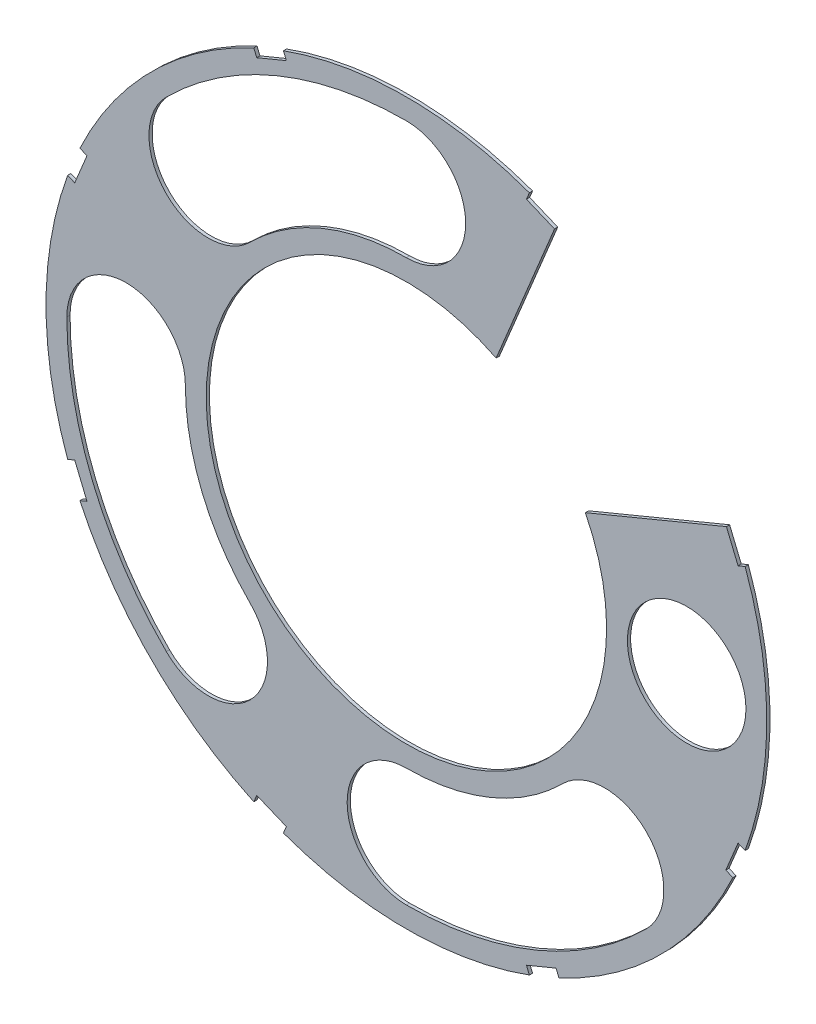
SolidWorks part; units mm, degrees
material "PTFE (general)"
ref_plane "Front Plane" through (0, 0, 0) normal (0, 0, 1) x (1, 0, 0)
ref_plane "Top Plane" through (0, 0, 0) normal (0, 1, 0) x (1, 0, 0)
ref_plane "Right Plane" through (0, 0, 0) normal (1, 0, 0) x (0, 0, -1)
sketch "Sketch4" plane through (0, 0, 0) normal (0, 0, 1) x (1, 0, 0)
  circle A0 centre (0, 0) radius 28.575
  dimension "D1" = 57.15
extrude "Boss-Extrude2" add sketch "Sketch4" along normal blind 0.254
sketch "Sketch5" plane through (0, 0, 0.254) normal (0, 0, 1) x (1, 0, 0)
  circle A0 centre (0, 0) radius 15.875
  circle A1 centre (0, 0) radius 28.575 construction
  dimension "D1" = 12.7
extrude "Cut-Extrude5" cut sketch "Sketch5" against normal through all
sketch "Sketch6" plane through (0, 0, 0.254) normal (0, 0, 1) x (1, 0, 0)
  line L0 (0, 0) -> (22.225, 0) construction
  line L1 (0, 0) -> (20.2056, -20.2056) construction
  line L2 (0, 0) -> (0, -28.575) construction
  line L3 (0, 0) -> (0, -28.575) construction
  line L4 (0, 0) -> (20.2056, -20.2056) construction
  line L5 (0, 0) -> (-20.2056, -20.2056) construction
  line L6 (0, 0) -> (-20.2056, -20.2056) construction
  line L7 (0, 0) -> (-28.575, 0) construction
  line L8 (0, 0) -> (-28.575, 0) construction
  line L9 (0, 0) -> (-20.2056, 20.2056) construction
  line L10 (0, 0) -> (-20.2056, 20.2056) construction
  line L11 (0, 0) -> (0, 28.575) construction
  line L12 (0, 0) -> (0, 28.575) construction
  line L13 (0, 0) -> (12.3928, -12.3928) construction
  line L14 (0, 0) -> (-12.3928, -12.3928) construction
  circle A0 centre (22.225, 0) radius 4.699
  circle A1 centre (0, 0) radius 28.575 construction
  arc A2 (19.0381, -19.0381) -> (12.3928, -12.3928) centre (15.7154, -15.7154) ccw
  arc A3 (12.3928, -12.3928) -> (0, -17.526) centre (0, 0) cw
  arc A4 (0, -17.526) -> (0, -26.924) centre (0, -22.225) ccw
  arc A5 (0, -26.924) -> (19.0381, -19.0381) centre (0, 0) ccw
  arc A6 (-19.0381, -19.0381) -> (-12.3928, -12.3928) centre (-15.7154, -15.7154) ccw
  arc A7 (-12.3928, -12.3928) -> (-17.526, 0) centre (0, 0) cw
  arc A8 (-26.924, 0) -> (-19.0381, -19.0381) centre (0, 0) ccw
  arc A9 (-17.526, 0) -> (-26.924, 0) centre (-22.225, 0) ccw
  arc A10 (-19.0381, 19.0381) -> (-12.3928, 12.3928) centre (-15.7154, 15.7154) ccw
  arc A11 (-12.3928, 12.3928) -> (0, 17.526) centre (0, 0) cw
  arc A12 (0, 26.924) -> (-19.0381, 19.0381) centre (0, 0) ccw
  arc A13 (0, 17.526) -> (0, 26.924) centre (0, 22.225) ccw
  circle A16 centre (0, 0) radius 15.875 construction
  point P4 (15.7154, -15.7154)
  point P11 (0, -22.225)
  point P13 (-15.7154, -15.7154)
  point P27 (-22.225, 0)
  point P30 (0, 0)
  point P36 (-15.7154, 15.7154)
  point P41 (0, 22.225)
  dimension "D2" = 9.398
  dimension "D3" = 45
  dimension "D4" = 90
  dimension "D1" = 6.35
  dimension "D6" = 6.35
  dimension "D7" = 9.398
  dimension "D8" = 4.699
  dimension "D9" = 4.699
  dimension "D5" = 6.35
  dimension "D10" = 90
extrude "Cut-Extrude6" cut sketch "Sketch6" against normal through all
sketch "Sketch8" plane through (0, 0, 0.254) normal (0, 0, 1) x (1, 0, 0)
  line L0 (0, 0) -> (26.3999, 10.9352) construction
  line L1 (0, 0) -> (10.9352, 26.3999) construction
  line L2 (11.7482, 25.3758) -> (9.5188, 26.2992)
  line L3 (25.3758, 11.7482) -> (26.2992, 9.5188)
  line L4 (26.8598, 9.751) -> (26.2992, 9.5188)
  line L5 (9.751, 26.8598) -> (9.5188, 26.2992)
  line L6 (0, 0) -> (28.575, 0) construction
  line L7 (-10.0049, 27.4725) -> (-12.3515, 26.5005)
  line L8 (-10.0049, 27.4725) -> (-9.5188, 26.2992)
  line L9 (-12.3515, 26.5005) -> (-11.8655, 25.3272)
  line L10 (-9.5188, 26.2992) -> (-11.8655, 25.3272)
  line L11 (-12.3515, 26.5005) -> (-9.5188, 26.2992) construction
  line L12 (-10.0049, 27.4725) -> (-11.8655, 25.3272) construction
  line L13 (-26.5005, 12.3515) -> (-27.4725, 10.0049)
  line L14 (-26.5005, 12.3515) -> (-25.3272, 11.8655)
  line L15 (-25.3272, 11.8655) -> (-26.2992, 9.5188)
  line L16 (-27.4725, 10.0049) -> (-26.2992, 9.5188)
  line L17 (-26.5005, 12.3515) -> (-26.2992, 9.5188) construction
  line L18 (-27.4725, 10.0049) -> (-25.3272, 11.8655) construction
  line L19 (-27.4725, -10.0049) -> (-26.5005, -12.3515)
  line L20 (-27.4725, -10.0049) -> (-26.2992, -9.5188)
  line L21 (-26.2992, -9.5188) -> (-25.3272, -11.8655)
  line L22 (-26.5005, -12.3515) -> (-25.3272, -11.8655)
  line L23 (-27.4725, -10.0049) -> (-25.3272, -11.8655) construction
  line L24 (-26.5005, -12.3515) -> (-26.2992, -9.5188) construction
  line L25 (-12.3515, -26.5005) -> (-10.0049, -27.4725)
  line L26 (-12.3515, -26.5005) -> (-11.8655, -25.3272)
  line L27 (-11.8655, -25.3272) -> (-9.5188, -26.2992)
  line L28 (-10.0049, -27.4725) -> (-9.5188, -26.2992)
  line L29 (-12.3515, -26.5005) -> (-9.5188, -26.2992) construction
  line L30 (-10.0049, -27.4725) -> (-11.8655, -25.3272) construction
  line L31 (10.0049, -27.4725) -> (12.3515, -26.5005)
  line L32 (10.0049, -27.4725) -> (9.5188, -26.2992)
  line L33 (9.5188, -26.2992) -> (11.8655, -25.3272)
  line L34 (12.3515, -26.5005) -> (11.8655, -25.3272)
  line L35 (10.0049, -27.4725) -> (11.8655, -25.3272) construction
  line L36 (12.3515, -26.5005) -> (9.5188, -26.2992) construction
  line L37 (26.5005, -12.3515) -> (27.4725, -10.0049)
  line L38 (26.5005, -12.3515) -> (25.3272, -11.8655)
  line L39 (25.3272, -11.8655) -> (26.2992, -9.5188)
  line L40 (27.4725, -10.0049) -> (26.2992, -9.5188)
  line L41 (26.5005, -12.3515) -> (26.2992, -9.5188) construction
  line L42 (27.4725, -10.0049) -> (25.3272, -11.8655) construction
  line L43 (14.1911, 7.1153) -> (25.3758, 11.7482)
  line L44 (7.1153, 14.1911) -> (11.7482, 25.3758)
  circle A0 centre (0, 0) radius 28.575 construction
  arc A1 (14.1911, 7.1153) -> (7.1153, 14.1911) centre (0, 0) ccw
  circle A2 centre (0, 0) radius 15.875 construction
  arc A3 (26.8598, 9.751) -> (9.751, 26.8598) centre (0, 0) ccw
  point P3 (-10.9352, 26.3999)
  point P11 (-26.3999, 10.9352)
  point P20 (-26.3999, -10.9352)
  point P25 (-10.9352, -26.3999)
  point P26 (0, 0)
  point P31 (10.9352, -26.3999)
  point P36 (26.3999, -10.9352)
  point P46 (0, 0)
  dimension "D4" = 90
  dimension "D19" = 28.575
  dimension "D2" = 67.5
  dimension "D3" = 22.5
  dimension "D5" = 1.27
  dimension "D6" = 2.54
  dimension "D7" = 1.27
  dimension "D8" = 2.413
  dimension "D9" = 0.635
  dimension "D10" = 112.5
  dimension "D12" = 90
  dimension "D13" = 90
  dimension "D14" = 0.635
  dimension "D15" = 2.413
  dimension "D16" = 270
  dimension "D17" = 0.635
  dimension "D18" = 0.635
  dimension "D20" = 1.27
  dimension "D21" = 22.5
  dimension "D22" = 1.27
  dimension "D11" = 6
extrude "Cut-Extrude11" cut sketch "Sketch8" against normal through all
